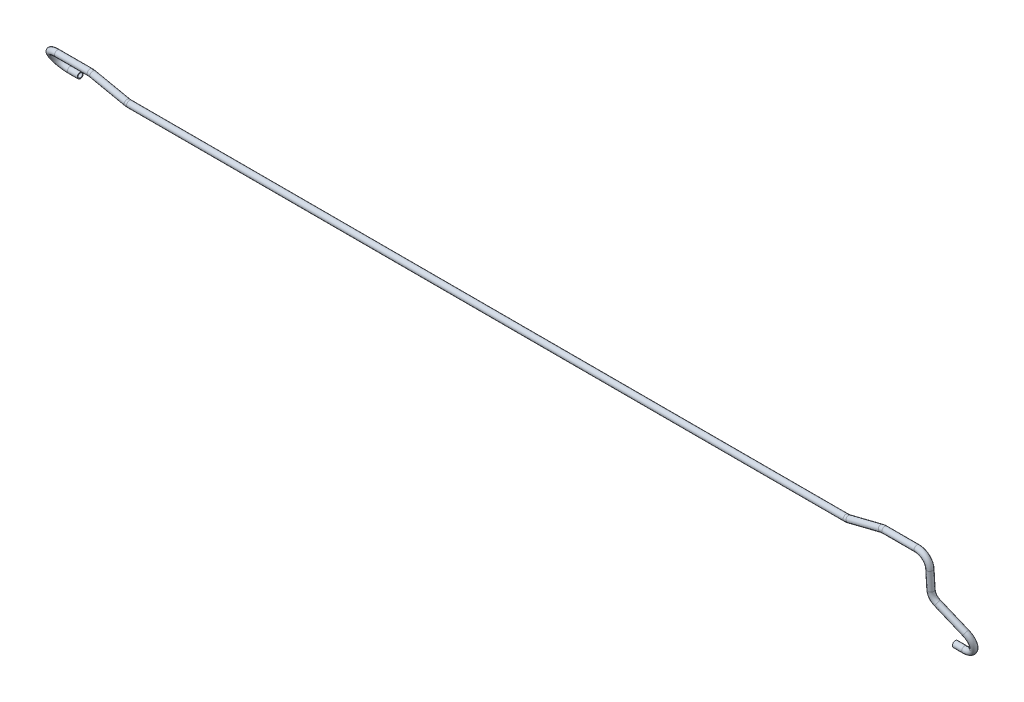
SolidWorks part; units mm, degrees
ref_plane "Plane1" through (0, 0, 0) normal (0, 0, 1) x (1, 0, 0)
ref_plane "Plane2" through (0, 0, 0) normal (0, 1, 0) x (1, 0, 0)
ref_plane "Plane3" through (0, 0, 0) normal (1, 0, 0) x (0, 0, -1)
sketch3d "3DSketch1"
  line L0 (0, 0, 0) -> (125, 0, 0) construction
  line L1 (125, 0, 0) -> (125, 0, 33) construction
  line L2 (125, 0, 33) -> (125, 112, 33) construction
  line L3 (0, 0, 0) -> (25.3283, 0, 0)
  line L4 (125, 112, 33) -> (-32, 112, 33) construction
  line L5 (-65, 212, 39) -> (-152.4229, 212, 39)
  line L6 (-157, 212, 39) -> (-157, 184, 39) construction
  line L7 (-18.3784, 102.2827, 30.1369) -> (45.0213, 57.0548, 16.8108)
  line L8 (-32, 128.9452, 34.0167) -> (-32, 179.0592, 37.0236)
  line L9 (-157, 184, 35) -> (-257, 184, 35) construction
  line L10 (-252.5957, 185.2332, 35.1762) -> (-161.4043, 210.7668, 38.8238)
  line L11 (-2210.5, 184, 35) -> (-2210.5, 205, 35) construction
  line L12 (-261.5771, 184, 35) -> (-2207.0724, 184, 35)
  line L13 (-2210.5, 205, 35) -> (-2435.5, 205, 35) construction
  line L14 (-2435.5, 205, 35) -> (-2435.5, 149.0447, 35) construction
  line L15 (-2435.5, 149.0447, 35) -> (-2435.5, 149.0447, 0) construction
  line L16 (-2402.5, 149.0447, 0) -> (-2375.5, 149.0447, 0)
  line L17 (-2435.5, 149.0447, 0) -> (-2435.5, 205, 35) construction
  line L18 (-2402.5, 205, 35) -> (-2313.9276, 205, 35)
  line L19 (-2307.1455, 204.2956, 35) -> (-2213.8545, 184.7044, 35)
  line L20 (-157, 184, 35) -> (-157, 184, 39) construction
  line L21 (-32, 212, 39) -> (-32, 112, 39) construction
  line L22 (-32, 112, 39) -> (-32, 112, 33) construction
  arc A0 (25.3283, 0, 0) -> (45.0213, 57.0548, 16.8108) centre (25.3283, 31.6546, 9.3268) ccw
  arc A1 (-32, 179.0592, 37.0236) -> (-65, 212, 39) centre (-65, 179.0592, 37.0236) ccw
  arc A2 (-18.3784, 102.2827, 30.1369) -> (-32, 128.9452, 34.0167) centre (0.5488, 129.2709, 28.588) ccw
  arc A3 (-152.4229, 212, 39) -> (-161.4043, 210.7668, 38.8238) centre (-152.4229, 179.3317, 34.3331) ccw
  arc A4 (-2402.5, 205, 35) -> (-2402.5, 149.0447, 0) centre (-2402.5, 177.0223, 17.5) ccw
  arc A6 (-2213.8545, 184.7044, 35) -> (-2207.0724, 184, 35) centre (-2207.0724, 217, 35) ccw
  arc A7 (-252.5957, 185.2332, 35.1762) -> (-261.5771, 184, 35) centre (-261.5771, 216.6683, 39.6669) ccw
  arc A8 (-2313.9276, 205, 35) -> (-2307.1455, 204.2956, 35) centre (-2313.9276, 172, 35) ccw
  point P9 (125, 0, 0)
  point P12 (25.3283, 22.3278, 40.9813)
  point P18 (-32, 212, 39)
  point P21 (-32, 112, 33)
  point P23 (-4.8897, 131.2203, -3.9024)
  point P24 (-65, 177.0828, 69.9643)
  point P27 (-157, 212, 39)
  point P29 (-152.4229, 174.6648, 67.0014)
  point P38 (-2402.5, 159.5223, 45.4777)
  point P42 (-2435.5, 205, 35)
  point P49 (-2210.5, 184, 35)
  point P51 (-257, 184, 35)
  point P53 (-261.5771, 221.3352, 6.9986)
  point P55 (-2207.0724, 217, 68)
  point P58 (-2310.5, 205, 35)
  point P59 (-2313.9276, 172, 2)
  dimension "D4" = 157
  dimension "D6" = 28
  dimension "D7" = 33
  dimension "D8" = 100
  dimension "D9" = 33
  dimension "D13" = 33
  dimension "D18" = 35
  dimension "D19" = 60
  dimension "D20" = 2178.5
  dimension "D11" = 33
  dimension "D12" = 33
  dimension "D21" = 4
  dimension "D22" = 6
  dimension "D23" = 33
  dimension "D24" = 33
  dimension "D1" = 125
  dimension "D2" = 112
  dimension "D3" = 33
  dimension "D5" = 100
  dimension "D10" = 125
  dimension "D14" = 100
  dimension "D15" = 21
  dimension "D16" = 225
  dimension "D17" = 55.9553
  dimension "D26" = 25.3283
  dimension "D25" = 66
ref_plane "Plane4" through (0, 0, 0) normal (1, 0, 0) x (0, 0, -1)
sketch "Sketch1" plane through (0, 0, 0) normal (1, 0, 0) x (0, 0, -1)
  circle A0 centre (0, 0) radius 8
  circle A1 centre (0, 0) radius 6
  dimension "D1" = 12
  dimension "D2" = 16
sweep "Sweep1" add profiles "Sketch1" path "3DSketch1"
